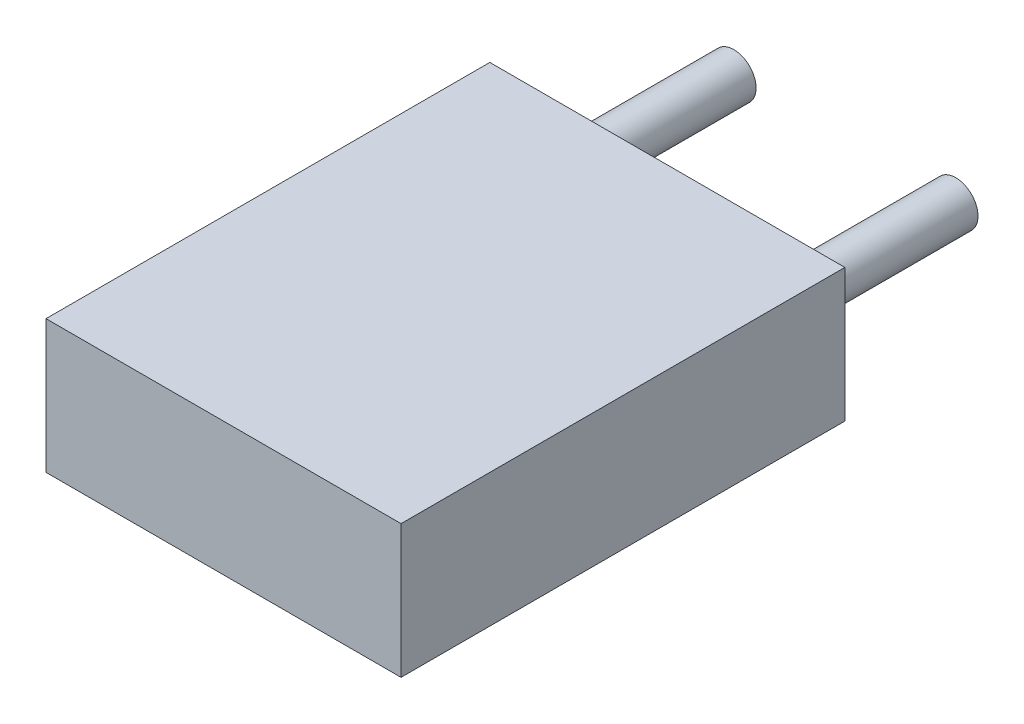
SolidWorks part; units mm, degrees
ref_plane "Front Plane" through (0, 0, 0) normal (0, 0, 1) x (1, 0, 0)
ref_plane "Top Plane" through (0, 0, 0) normal (0, 1, 0) x (1, 0, 0)
ref_plane "Right Plane" through (0, 0, 0) normal (1, 0, 0) x (0, 0, -1)
sketch "Sketch1" plane through (0, 0, 0) normal (0, 0, 1) x (1, 0, 0)
  line L0 (-0.75, 0.75) -> (-0.75, -0.75)
  line L1 (-0.75, -0.75) -> (3.25, -0.75)
  line L2 (3.25, -0.75) -> (3.25, 0.75)
  line L3 (3.25, 0.75) -> (-0.75, 0.75)
extrude "Component_Outline" add sketch "Sketch1" along normal blind 5 separate body
sketch "Sketch2" plane through (0, 0, 0) normal (0, 0, 1) x (1, 0, 0)
  circle A0 centre (0, 0) radius 0.25
extrude "1" add sketch "Sketch2" against normal blind 2 separate body
sketch "Sketch3" plane through (0, 0, 0) normal (0, 0, 1) x (1, 0, 0)
  circle A0 centre (2.5, 0) radius 0.25
extrude "2" add sketch "Sketch3" against normal blind 2 separate body
sketch3d "3DSketch1"
  line L0 (0, 0, 0) -> (1, 0, 0)
  line L1 (0, 0, 0) -> (0, 1, 0)
  line L2 (0, 0, 0) -> (0, 0, 1)
  point P0 (0, 0, 0)
